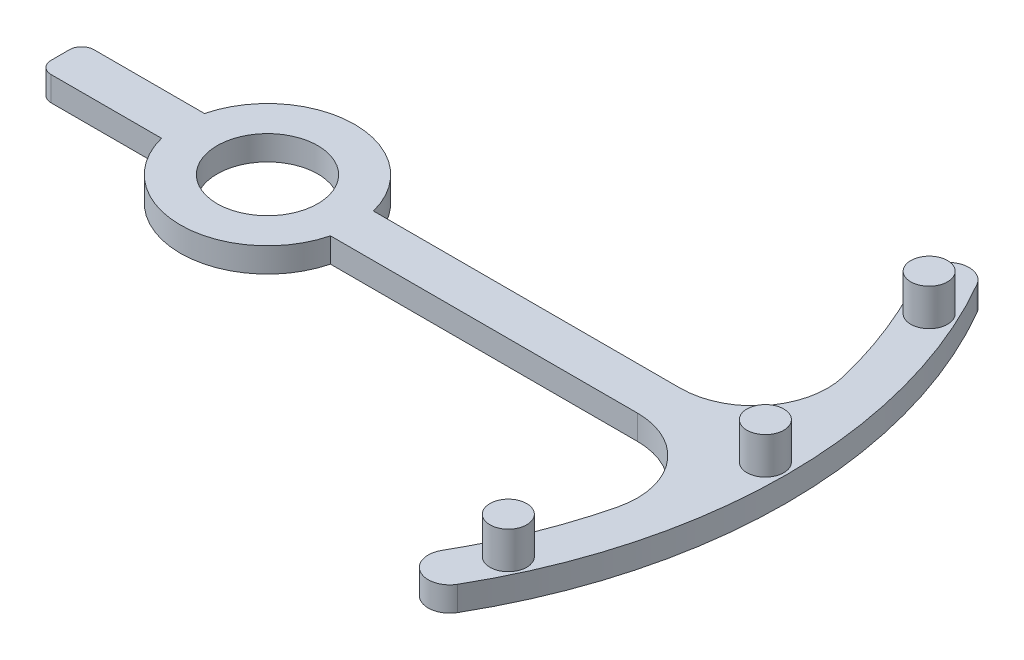
SolidWorks part; units mm, degrees
ref_plane "Front Plane" through (0, 0, 0) normal (0, 0, 1) x (1, 0, 0)
ref_plane "Top Plane" through (0, 0, 0) normal (0, 1, 0) x (1, 0, 0)
ref_plane "Right Plane" through (0, 0, 0) normal (1, 0, 0) x (0, 0, -1)
sketch "Sketch1" plane through (0, 0, 0) normal (0, 1, 0) x (1, 0, 0)
  line L0 (-17.8112, 0) -> (69.2303, 0) construction
  line L1 (6.881, 1.75) -> (31.881, 1.75)
  line L2 (0, 0) -> (33.6099, 19.4047) construction
  line L4 (6.881, -1.75) -> (31.881, -1.75)
  line L5 (-16.8813, 0.7486) -> (-16.8813, -0.7486)
  line L6 (-6.8813, -1.7486) -> (-15.8813, -1.7486)
  line L7 (-6.8813, 1.7486) -> (-15.8813, 1.7486)
  circle A0 centre (0, 0) radius 4.1
  arc A1 (6.881, 1.75) -> (-6.8813, 1.7486) centre (0, 0) ccw
  arc A2 (33.6099, -19.4047) -> (37.7112, -9.1673) centre (0, 0) ccw
  arc A3 (36.641, -21.1547) -> (36.641, 21.1547) centre (0, 0) ccw
  arc A4 (37.7112, 9.1673) -> (33.6099, 19.4047) centre (0, 0) ccw
  arc A5 (33.6099, 19.4047) -> (36.641, 21.1547) centre (35.1255, 20.2797) cw
  arc A6 (33.6099, -19.4047) -> (36.641, -21.1547) centre (35.1255, -20.2797) ccw
  arc A7 (-6.8813, -1.7486) -> (6.881, -1.75) centre (0, 0) ccw
  arc A8 (-15.8813, 1.7486) -> (-16.8813, 0.7486) centre (-15.8813, 0.7486) ccw
  arc A9 (-15.8813, -1.7486) -> (-16.8813, -0.7486) centre (-15.8813, -0.7486) cw
  arc A10 (37.7112, 9.1673) -> (31.881, 1.75) centre (31.881, 7.75) cw
  arc A11 (37.7112, -9.1673) -> (31.881, -1.75) centre (31.881, -7.75) ccw
  point P20 (-16.8813, 1.7486)
  point P26 (-16.8813, -1.7486)
  point P27 (38.7699, 1.75)
  dimension "D1" = 1
  dimension "D3" = 6
  dimension "D4" = 6
  dimension "D2" = 1
  dimension "D5" = 8.2
  dimension "D7" = 7.1
  dimension "D9" = 30
  dimension "D6" = 10
  dimension "D8" = 25
  dimension "D10" = 3.5
  dimension "D11" = 38.8094
extrude "Boss-Extrude1" add sketch "Sketch1" along normal blind 2
sketch "Sketch2" plane through (0, 2, 0) normal (0, 1, 0) x (1, 0, 0)
  line L0 (0, 0) -> (46.512, 21.6889) construction
  line L1 (0, 0) -> (52.2989, 0) construction
  circle A0 centre (36.7593, 17.1412) radius 1.5
  circle A1 centre (40.5594, 0) radius 1.5
  circle A2 centre (36.7593, -17.1412) radius 1.5
  point P10 (0, 0)
  dimension "D1" = 25
extrude "Boss-Extrude2" add sketch "Sketch2" along normal blind 3
